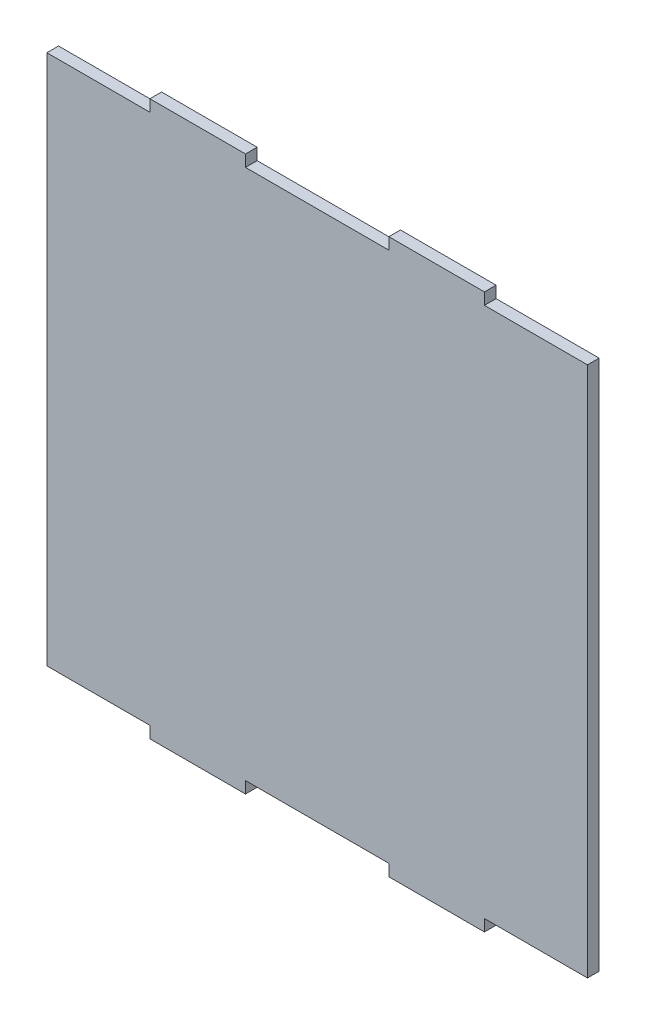
SolidWorks part; units mm, degrees
ref_plane "Alzado" through (0, 0, 0) normal (0, 0, 1) x (1, 0, 0)
ref_plane "Planta" through (0, 0, 0) normal (0, 1, 0) x (1, 0, 0)
ref_plane "Vista lateral" through (0, 0, 0) normal (1, 0, 0) x (0, 0, -1)
sketch "Croquis1" plane through (0, 0, 0) normal (0, 0, 1) x (1, 0, 0)
  line L0 (0, 0) -> (0, -55.56) construction
  line L1 (-56.56, -55.56) -> (-35, -55.56)
  line L2 (-56.56, -55.56) -> (-56.56, 55.56)
  line L3 (-56.56, 55.56) -> (-35, 55.56)
  line L4 (56.56, -55.56) -> (56.56, 55.56)
  line L5 (-56.56, -55.56) -> (56.56, 55.56) construction
  line L6 (-56.56, 55.56) -> (56.56, -55.56) construction
  line L7 (35, -55.56) -> (56.56, -55.56)
  line L8 (35, -58) -> (15, -58)
  line L9 (35, -58) -> (35, -55.56)
  line L10 (-15, -58) -> (-15, -55.56)
  line L11 (15, -58) -> (15, -55.56)
  line L12 (35, -58) -> (15, -55.56) construction
  line L13 (35, -55.56) -> (15, -58) construction
  line L14 (-35, -58) -> (-15, -58)
  line L15 (-35, -58) -> (-35, -55.56)
  line L16 (-15, -55.56) -> (15, -55.56)
  line L17 (35, 55.56) -> (56.56, 55.56)
  line L18 (35, 58) -> (15, 58)
  line L19 (35, 58) -> (35, 55.56)
  line L20 (-15, 58) -> (-15, 55.56)
  line L21 (15, 58) -> (15, 55.56)
  line L22 (35, 58) -> (15, 55.56) construction
  line L23 (35, 55.56) -> (15, 58) construction
  line L24 (-35, 58) -> (-15, 58)
  line L25 (-35, 58) -> (-35, 55.56)
  line L26 (-15, 55.56) -> (15, 55.56)
  point P0 (0, 0)
  point P6 (25, -56.78)
  point P17 (25, 56.78)
  dimension "D1" = 111.12
  dimension "D2" = 113.12
  dimension "D3" = 15
  dimension "D4" = 20
  dimension "D5" = 2.44
  dimension "D6" = 15
  dimension "D7" = 20
  dimension "D8" = 2.44
extrude "Saliente-Extruir1" add sketch "Croquis1" along normal blind 2.44
